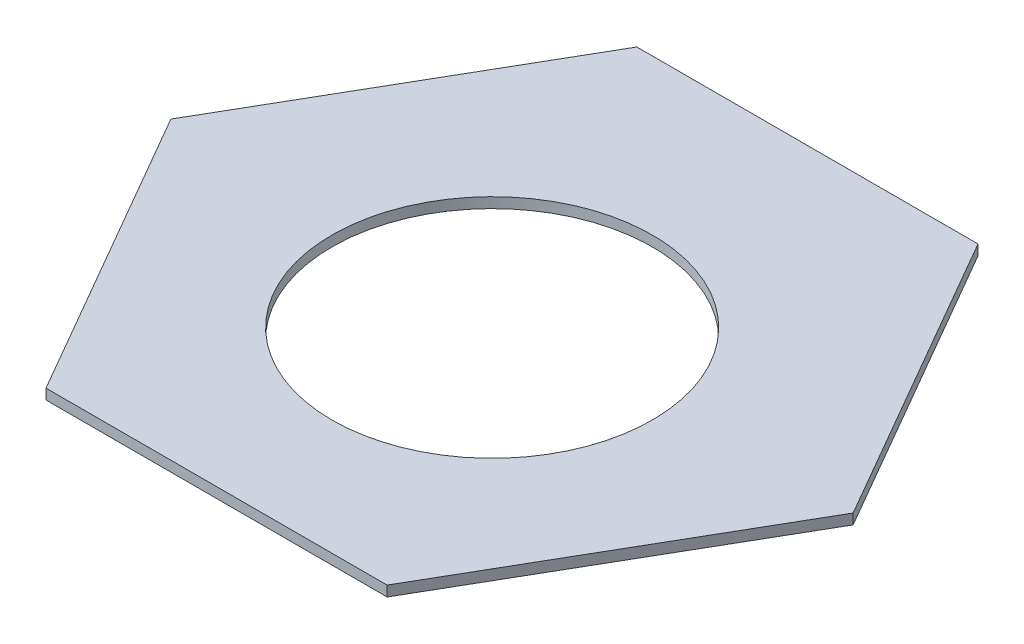
SolidWorks part; units mm, degrees
ref_plane "Front Plane" through (0, 0, 0) normal (0, 0, 1) x (1, 0, 0)
ref_plane "Top Plane" through (0, 0, 0) normal (0, 1, 0) x (1, 0, 0)
ref_plane "Right Plane" through (0, 0, 0) normal (1, 0, 0) x (0, 0, -1)
sketch "Sketch1" plane through (0, 0, 0) normal (0, 1, 0) x (1, 0, 0)
  line L1 (165, 0) -> (82.5, 142.8942)
  line L2 (82.5, 142.8942) -> (-82.5, 142.8942)
  line L3 (-82.5, 142.8942) -> (-165, 0)
  line L4 (-165, 0) -> (-82.5, -142.8942)
  line L5 (-82.5, -142.8942) -> (82.5, -142.8942)
  line L6 (82.5, -142.8942) -> (165, 0)
  circle A0 centre (0, 0) radius 142.8942 construction
  circle A1 centre (0, -9.6058) radius 77.5
  dimension "D2" = 155
  dimension "D3" = 152.5
  dimension "D1" = 165
extrude "Boss-Extrude1" add sketch "Sketch1" along normal blind 5
